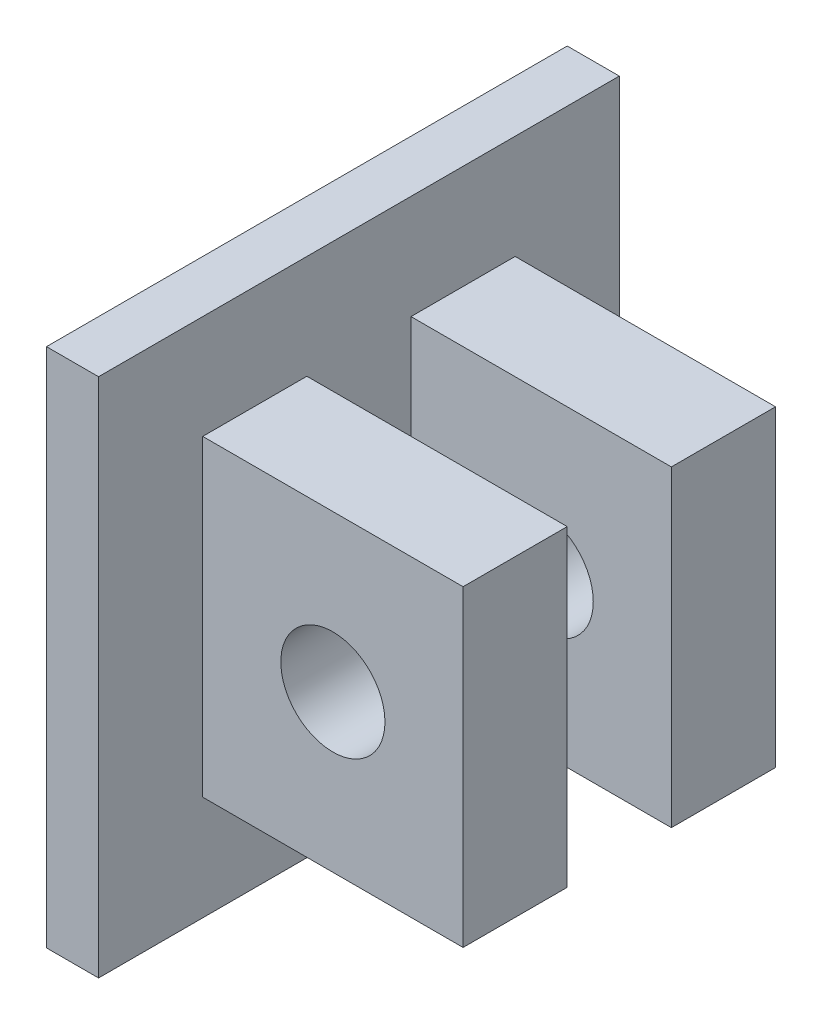
SolidWorks part; units mm, degrees
ref_plane "Front Plane" through (0, 0, 0) normal (0, 0, 1) x (1, 0, 0)
ref_plane "Top Plane" through (0, 0, 0) normal (0, 1, 0) x (1, 0, 0)
ref_plane "Right Plane" through (0, 0, 0) normal (1, 0, 0) x (0, 0, -1)
sketch "Sketch5" plane through (0, 0, 0) normal (1, 0, 0) x (0, 0, -1)
  line L1 (-50, -50) -> (50, -50)
  line L2 (-50, -50) -> (-50, 50)
  line L3 (-50, 50) -> (50, 50)
  line L4 (50, -50) -> (50, 50)
  line L5 (-50, -50) -> (50, 50) construction
  line L6 (-50, 50) -> (50, -50) construction
  point P0 (0, 0)
  dimension "D1" = 100
extrude "Boss-Extrude3" add sketch "Sketch5" along normal blind 10
sketch "Sketch6" plane through (10, 0, 0) normal (1, 0, 0) x (0, 0, -1)
  line L1 (-10, -29.9239) -> (-30, -29.9239)
  line L2 (-10, -29.9239) -> (-10, 30.0761)
  line L3 (-10, 30.0761) -> (-30, 30.0761)
  line L4 (-30, -29.9239) -> (-30, 30.0761)
  line L5 (30, -30) -> (10, -30)
  line L6 (30, -30) -> (30, 30)
  line L7 (30, 30) -> (10, 30)
  line L8 (10, -30) -> (10, 30)
  line L10 (-50, -50) -> (50, -50) construction
  point P11 (-94.717, 18.4073)
  dimension "D1" = 60
  dimension "D2" = 20
  dimension "D3" = 10
  dimension "D4" = 10
  dimension "D5" = 20.0761
  dimension "D6" = 20
extrude "Boss-Extrude4" add sketch "Sketch6" along normal blind 50
sketch "Sketch7" plane through (0, 0, 30) normal (0, 0, 1) x (1, 0, 0)
  line L0 (60, 30.0761) -> (10, 30.0761) construction
  line L2 (60, 30.0761) -> (60, -29.9239) construction
  circle A0 centre (35, 0.0761) radius 10
  point P2 (0, 0)
  point P7 (-76.0747, 55.943)
  dimension "D1" = 20
  dimension "D2" = 30
  dimension "D3" = 25
extrude "Cut-Extrude2" cut sketch "Sketch7" against normal blind 60
